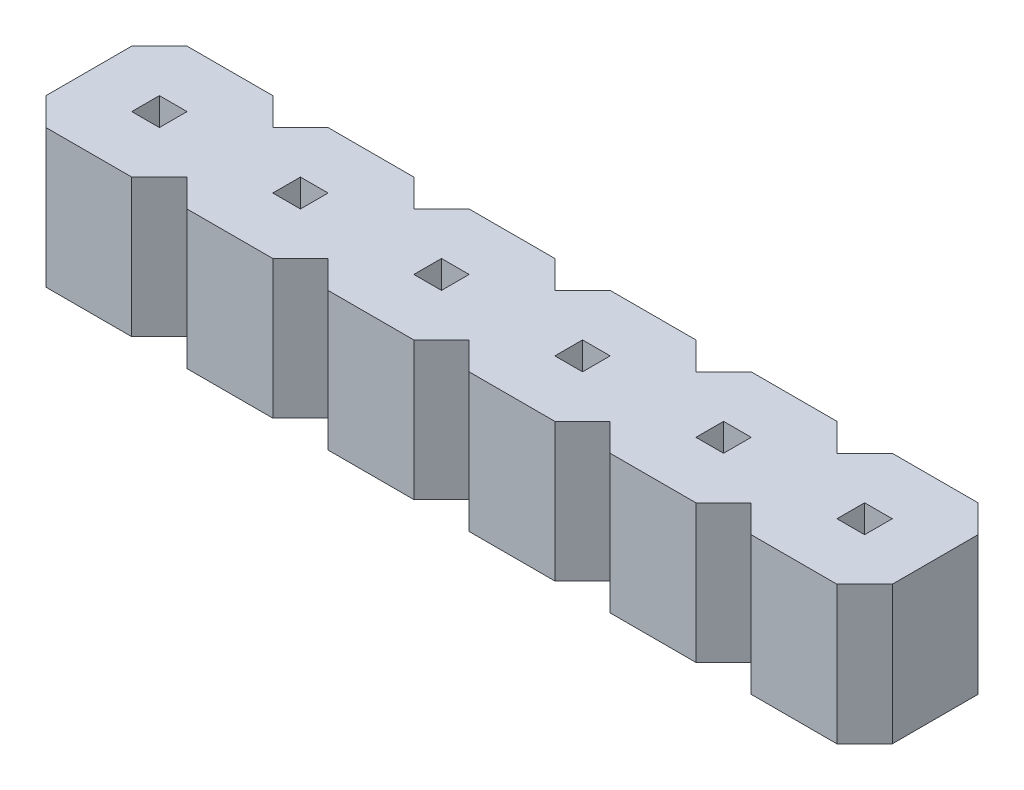
SolidWorks part; units mm, degrees
ref_plane "Front Plane" through (0, 0, 0) normal (0, 0, 1) x (1, 0, 0)
ref_plane "Top Plane" through (0, 0, 0) normal (0, 1, 0) x (1, 0, 0)
ref_plane "Right Plane" through (0, 0, 0) normal (1, 0, 0) x (0, 0, -1)
sketch "Sketch1" plane through (0, 0, 0) normal (0, 1, 0) x (1, 0, 0)
  line L6 (-0.775, 1.275) -> (-1.275, 0.775)
  line L36 (0.775, 1.275) -> (1.275, 0.775)
  line L37 (1.275, -0.775) -> (0.775, -1.275)
  line L38 (-1.275, -0.775) -> (-0.775, -1.275)
  line L44 (1.775, 1.275) -> (3.325, 1.275)
  line L45 (1.775, 1.275) -> (1.275, 0.775)
  line L60 (1.275, 1.275) -> (3.825, -1.275) construction
  line L61 (-0.775, 1.275) -> (0.775, 1.275)
  line L62 (-1.275, 0.775) -> (-1.275, -0.775)
  line L63 (-0.775, -1.275) -> (0.775, -1.275)
  line L65 (-1.275, 1.275) -> (1.275, -1.275) construction
  line L66 (-1.275, -1.275) -> (1.275, 1.275) construction
  line L67 (1.275, -1.275) -> (3.825, 1.275) construction
  line L71 (3.325, 1.275) -> (3.825, 0.775)
  line L73 (3.825, -0.775) -> (3.325, -1.275)
  line L74 (1.775, -1.275) -> (3.325, -1.275)
  line L75 (1.275, -0.775) -> (1.775, -1.275)
  line L77 (4.325, 1.275) -> (5.875, 1.275)
  line L78 (4.325, 1.275) -> (3.825, 0.775)
  line L79 (3.825, 1.275) -> (6.375, -1.275) construction
  line L80 (3.825, -1.275) -> (6.375, 1.275) construction
  line L81 (5.875, 1.275) -> (6.375, 0.775)
  line L83 (6.375, -0.775) -> (5.875, -1.275)
  line L84 (4.325, -1.275) -> (5.875, -1.275)
  line L85 (3.825, -0.775) -> (4.325, -1.275)
  line L87 (6.875, 1.275) -> (8.425, 1.275)
  line L89 (6.875, 1.275) -> (6.375, 0.775)
  line L90 (6.375, 1.275) -> (8.925, -1.275) construction
  line L91 (6.375, -1.275) -> (8.925, 1.275) construction
  line L95 (8.425, 1.275) -> (8.925, 0.775)
  line L97 (8.925, -0.775) -> (8.425, -1.275)
  line L98 (6.875, -1.275) -> (8.425, -1.275)
  line L99 (6.375, -0.775) -> (6.875, -1.275)
  line L101 (9.425, 1.275) -> (10.975, 1.275)
  line L102 (9.425, 1.275) -> (8.925, 0.775)
  line L103 (8.925, 1.275) -> (11.475, -1.275) construction
  line L104 (8.925, -1.275) -> (11.475, 1.275) construction
  line L105 (10.975, 1.275) -> (11.475, 0.775)
  line L107 (11.475, -0.775) -> (10.975, -1.275)
  line L108 (9.425, -1.275) -> (10.975, -1.275)
  line L109 (8.925, -0.775) -> (9.425, -1.275)
  line L111 (11.975, 1.275) -> (13.525, 1.275)
  line L113 (11.975, 1.275) -> (11.475, 0.775)
  line L114 (11.475, 1.275) -> (14.025, -1.275) construction
  line L115 (11.475, -1.275) -> (14.025, 1.275) construction
  line L119 (13.525, 1.275) -> (14.025, 0.775)
  line L120 (14.025, 0.775) -> (14.025, -0.775)
  line L121 (14.025, -0.775) -> (13.525, -1.275)
  line L122 (11.975, -1.275) -> (13.525, -1.275)
  line L123 (11.475, -0.775) -> (11.975, -1.275)
  line L186 (1.275, 0.775) -> (1.275, -0.775) [skipped]
  line L187 (3.825, 0.775) -> (3.825, -0.775) [skipped]
  line L188 (6.375, 0.775) -> (6.375, -0.775) [skipped]
  line L189 (11.475, 0.775) -> (11.475, -0.775) [skipped]
  line L190 (8.925, 0.775) -> (8.925, -0.775) [skipped]
  dimension "D1" = 2.55
  dimension "D2" = 6
extrude "Boss-Extrude1" add sketch "Sketch1" along normal mid plane 2.5
sketch "Sketch2" plane through (0, 1.25, 0) normal (0, 1, 0) x (1, 0, 0)
  line L0 (2.3, -0.25) -> (2.8, -0.25)
  line L1 (-0.25, -0.25) -> (0.25, -0.25)
  line L2 (-0.25, -0.25) -> (-0.25, 0.25)
  line L3 (-0.25, 0.25) -> (0.25, 0.25)
  line L4 (0.25, -0.25) -> (0.25, 0.25)
  line L5 (-0.25, -0.25) -> (0.25, 0.25) construction
  line L6 (-0.25, 0.25) -> (0.25, -0.25) construction
  line L7 (2.3, -0.25) -> (2.3, 0.25)
  line L8 (2.8, -0.25) -> (2.8, 0.25)
  line L9 (2.3, -0.25) -> (2.8, 0.25) construction
  line L10 (2.3, 0.25) -> (2.8, -0.25) construction
  line L11 (2.3, 0.25) -> (2.8, 0.25)
  line L12 (4.85, -0.25) -> (5.35, -0.25)
  line L13 (4.85, -0.25) -> (4.85, 0.25)
  line L14 (5.35, -0.25) -> (5.35, 0.25)
  line L15 (4.85, -0.25) -> (5.35, 0.25) construction
  line L16 (4.85, 0.25) -> (5.35, -0.25) construction
  line L17 (4.85, 0.25) -> (5.35, 0.25)
  line L18 (7.4, -0.25) -> (7.9, -0.25)
  line L19 (7.4, -0.25) -> (7.4, 0.25)
  line L20 (7.9, -0.25) -> (7.9, 0.25)
  line L21 (7.4, -0.25) -> (7.9, 0.25) construction
  line L22 (7.4, 0.25) -> (7.9, -0.25) construction
  line L23 (7.4, 0.25) -> (7.9, 0.25)
  line L24 (9.95, -0.25) -> (10.45, -0.25)
  line L25 (9.95, -0.25) -> (9.95, 0.25)
  line L26 (10.45, -0.25) -> (10.45, 0.25)
  line L27 (9.95, -0.25) -> (10.45, 0.25) construction
  line L28 (9.95, 0.25) -> (10.45, -0.25) construction
  line L29 (9.95, 0.25) -> (10.45, 0.25)
  line L30 (12.5, -0.25) -> (13, -0.25)
  line L31 (12.5, -0.25) -> (12.5, 0.25)
  line L32 (13, -0.25) -> (13, 0.25)
  line L33 (12.5, -0.25) -> (13, 0.25) construction
  line L34 (12.5, 0.25) -> (13, -0.25) construction
  line L35 (12.5, 0.25) -> (13, 0.25)
  point P0 (0, 0)
  point P7 (2.55, 0)
  point P12 (5.1, 0)
  point P17 (7.65, 0)
  point P22 (10.2, 0)
  point P27 (12.75, 0)
  dimension "D1" = 0.5
  dimension "D3" = 2.55
  dimension "D2" = 6
extrude "Cut-Extrude1" cut sketch "Sketch2" against normal through all
